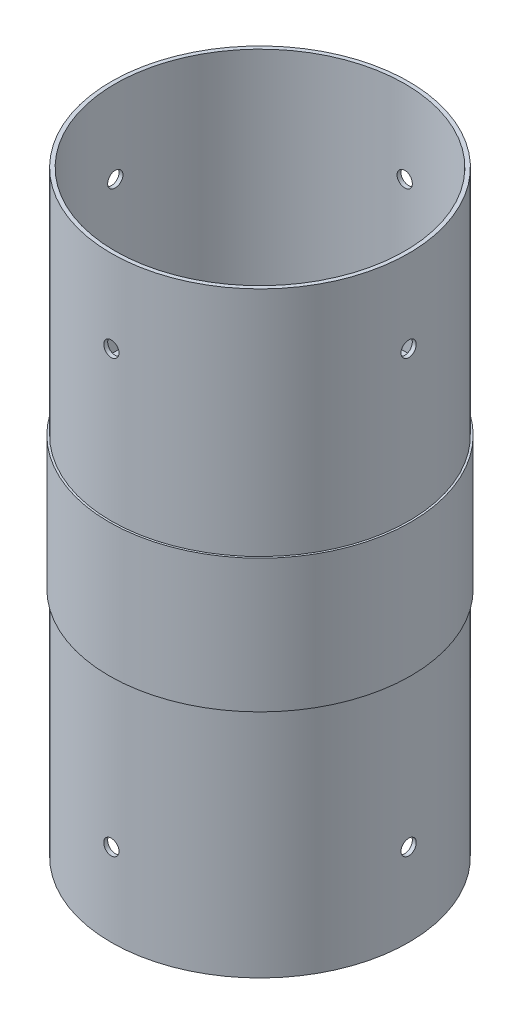
SolidWorks part; units mm, degrees
ref_plane "Front Plane" through (0, 0, 0) normal (0, 0, 1) x (1, 0, 0)
ref_plane "Top Plane" through (0, 0, 0) normal (0, 1, 0) x (1, 0, 0)
ref_plane "Right Plane" through (0, 0, 0) normal (1, 0, 0) x (0, 0, -1)
sketch "Sketch1" plane through (0, 0, 0) normal (0, 1, 0) x (1, 0, 0)
  circle A0 centre (0, 0) radius 37
  circle A1 centre (0, 0) radius 38
  dimension "D1" = 76
  dimension "D2" = 74
extrude "Boss-Extrude1" add sketch "Sketch1" along normal blind 152.4
ref_plane "Plane1" through (0, 76.2, 0) normal (0, 1, 0) x (1, 0, 0)
sketch "Sketch2" plane through (0, 76.2, 0) normal (0, 1, 0) x (1, 0, 0)
  circle A0 centre (0, 0) radius 38.5
  dimension "D1" = 77
extrude "Boss-Extrude2" add sketch "Sketch2" along normal blind 17 and the other way blind 17
sketch "Sketch3" plane through (0, 0, 0) normal (1, 0, 0) x (0, 0, -1)
  line L0 (0, 93.2) -> (0, 131.3) construction
  line L1 (38, 93.2) -> (-38, 93.2) construction
  circle A0 centre (0, 131.3) radius 1.95
  point P2 (0, 0)
  dimension "D2" = 3.9
  dimension "D1" = 38.1
  dimension "D3" = 38.5
extrude "Cut-Extrude1" cut sketch "Sketch3" against normal through all both and the other way through all
sketch "Sketch4" plane through (0, 0, 0) normal (0, 0, 1) x (1, 0, 0)
  line L0 (0, 93.2) -> (0, 131.3) construction
  line L1 (38, 93.2) -> (-38, 93.2) construction
  circle A0 centre (0, 131.3) radius 1.95
  dimension "D2" = 3.9
  dimension "D1" = 38.1
  dimension "D3" = 38.5
extrude "Cut-Extrude2" cut sketch "Sketch4" against normal through all both and the other way through all
mirror "Mirror1" about plane through (0, 76.2, 0) normal (0, 1, 0) of "Cut-Extrude2", "Cut-Extrude1"
